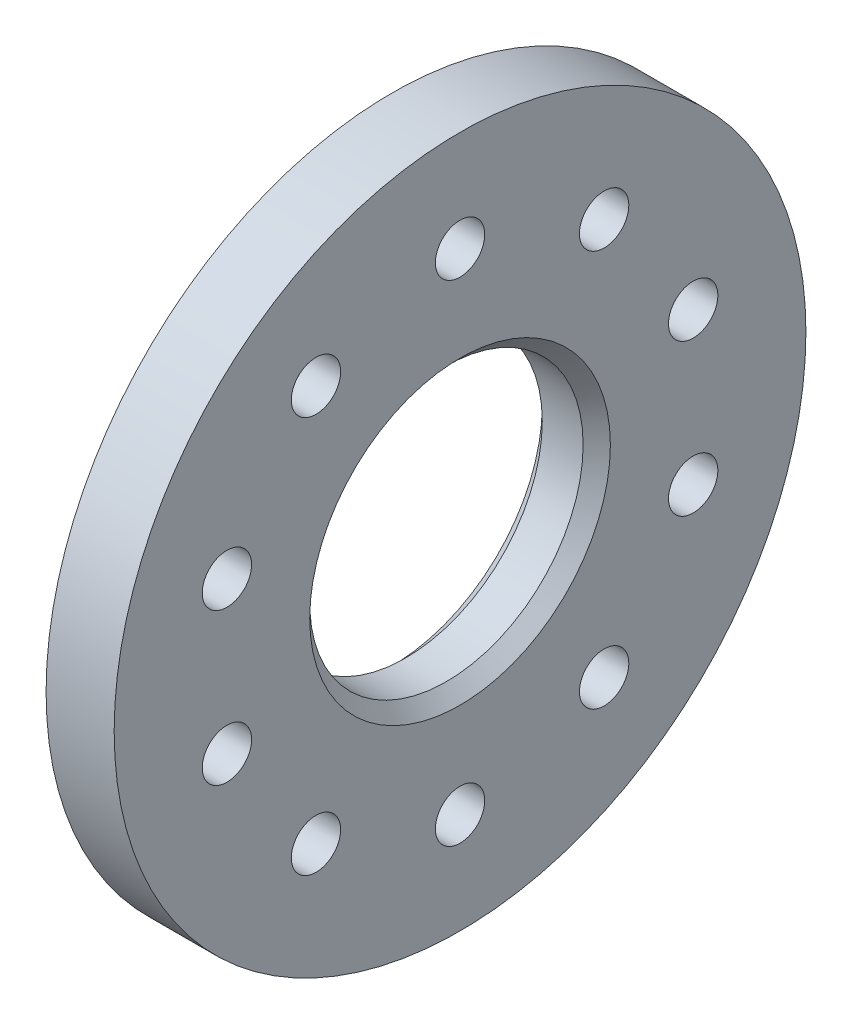
SolidWorks part; units mm, degrees
material "6061-T6 (SS)"
ref_plane "Front Plane" through (0, 0, 0) normal (0, 0, 1) x (1, 0, 0)
ref_plane "Top Plane" through (0, 0, 0) normal (0, 1, 0) x (1, 0, 0)
ref_plane "Right Plane" through (0, 0, 0) normal (1, 0, 0) x (0, 0, -1)
sketch "Sketch1" plane through (0, 0, 0) normal (1, 0, 0) x (0, 0, -1)
  circle A0 centre (0, 0) radius 57.15 construction
  circle A1 centre (0, 0) radius 80.645
  dimension "D1" = 114.3
  dimension "D2" = 161.29
extrude "Boss-Extrude1" add sketch "Sketch1" along normal mid plane 15.875
sketch "Sketch3" plane through (7.9375, 0, 0) normal (1, 0, 0) x (0, 0, -1)
  circle A0 centre (0, 0) radius 31.877
  dimension "D1" = 63.754
extrude "Cut-Extrude1" cut sketch "Sketch3" against normal through all
chamfer "Chamfer1" distance 3.175 angle 45 2 edges at (-7.9375, 0, -31.877) (7.9375, 0, -31.877)
sketch "Sketch5" plane through (7.9375, 0, 0) normal (1, 0, 0) x (0, 0, -1)
  line L0 (0, 0) -> (0, 57.15) construction
  circle A1 centre (0, 0) radius 57.15 construction
  circle A2 centre (0, 57.15) radius 5.7547
  dimension "D1" = 11.5094
extrude "Cut-Extrude2" cut sketch "Sketch5" against normal through all
pattern_circular "CirPattern1" count 5 over 360 about axis through (0, 0, 0) along (1, 0, 0) of "Cut-Extrude2"
sketch "Sketch6" plane through (7.9375, 0, 0) normal (1, 0, 0) x (0, 0, -1)
  line L0 (0, 0) -> (0, -57.15) construction
  circle A0 centre (0, 0) radius 57.15 construction
  circle A1 centre (0, -57.15) radius 5.7547
  dimension "D1" = 11.5094
extrude "Cut-Extrude3" cut sketch "Sketch6" against normal through all
pattern_circular "CirPattern2" count 5 over 360 about axis through (0, 0, 0) along (1, 0, 0) of "Cut-Extrude3"
